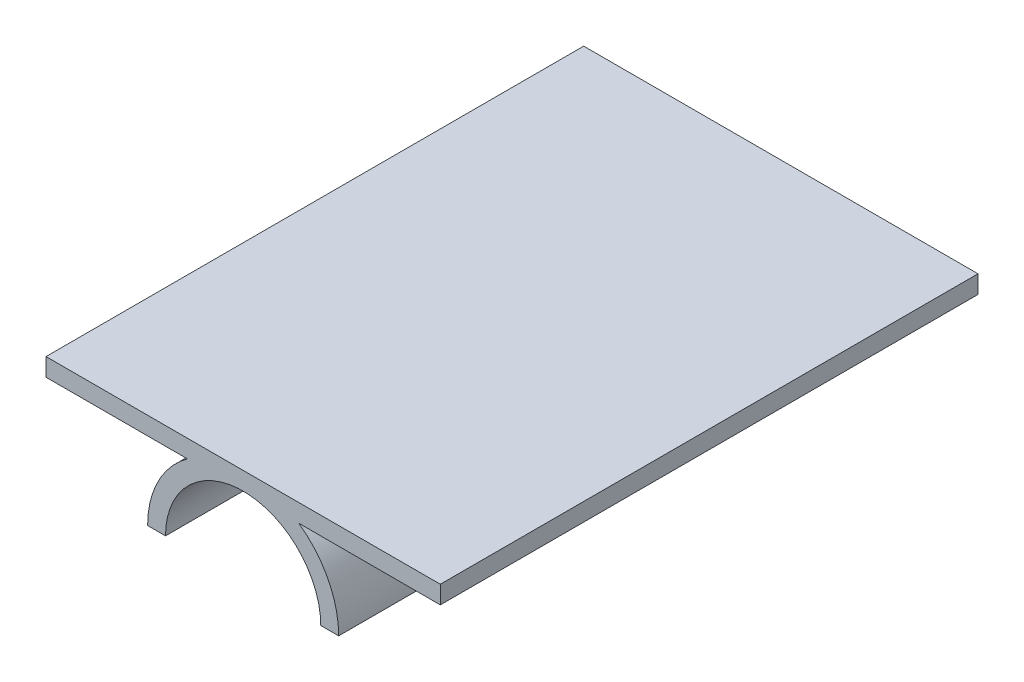
SolidWorks part; units mm, degrees
ref_plane "Front Plane" through (0, 0, 0) normal (0, 0, 1) x (1, 0, 0)
ref_plane "Top Plane" through (0, 0, 0) normal (0, 1, 0) x (1, 0, 0)
ref_plane "Right Plane" through (0, 0, 0) normal (1, 0, 0) x (0, 0, -1)
sketch "Sketch1" plane through (0, 0, 0) normal (0, 0, 1) x (1, 0, 0)
  line L0 (-11, 0) -> (-13.54, 0)
  line L1 (11, 0) -> (13.54, 0)
  line L2 (-7.895, 11) -> (-27.94, 11)
  line L3 (27.94, 11) -> (7.895, 11)
  line L4 (27.94, 11) -> (27.94, 13.54)
  line L5 (27.94, 13.54) -> (-27.94, 13.54)
  line L6 (-27.94, 11) -> (-27.94, 13.54)
  arc A0 (-13.54, 0) -> (-7.895, 11) centre (0, 0) cw
  arc A1 (-11, 0) -> (11, 0) centre (0, 0) cw
  arc A2 (7.895, 11) -> (13.54, 0) centre (0, 0) cw
  dimension "D1" = 11
  dimension "D2" = 2.54
  dimension "D3" = 27.94
  dimension "D4" = 27.94
  dimension "D5" = 2.54
extrude "Boss-Extrude1" add sketch "Sketch1" along normal blind 76.2
equation "\"D3@Sketch1\"=\"D4@Sketch1\""
